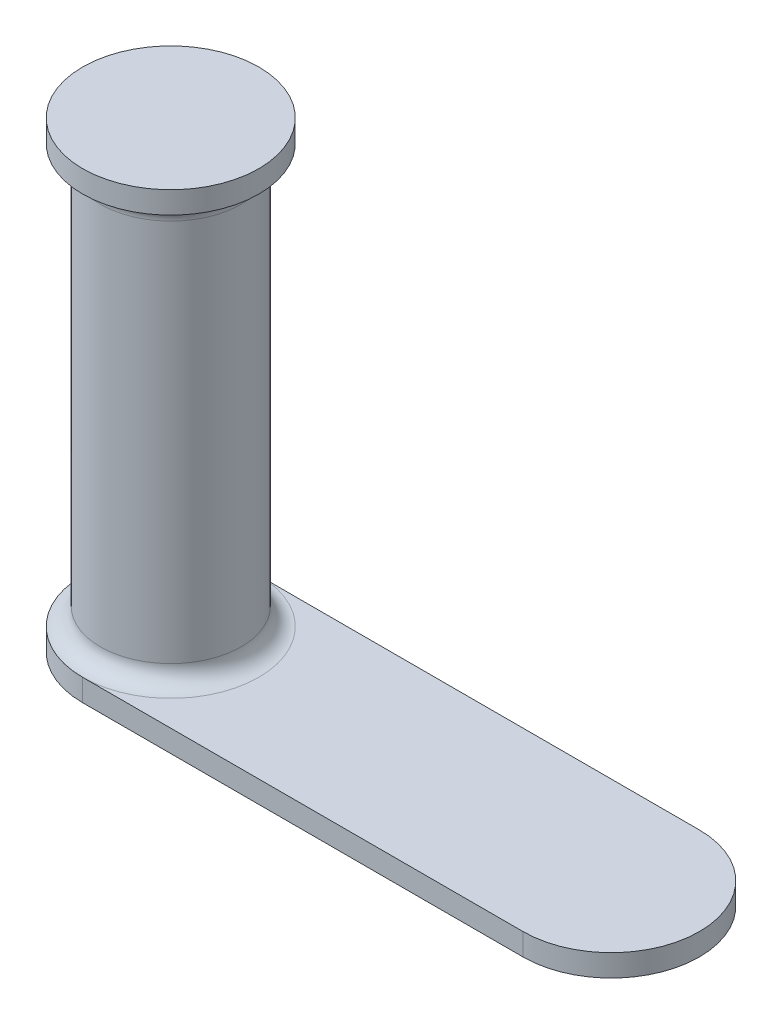
SolidWorks part; units mm, degrees
ref_plane "前视基准面" through (0, 0, 0) normal (0, 0, 1) x (1, 0, 0)
ref_plane "上视基准面" through (0, 0, 0) normal (0, 1, 0) x (1, 0, 0)
ref_plane "右视基准面" through (0, 0, 0) normal (1, 0, 0) x (0, 0, -1)
sketch "草图1" plane through (0, 0, 0) normal (0, 0, 1) x (1, 0, 0)
  line L0 (0, 60.1847) -> (0, -39.8153)
  line L1 (0, -39.8153) -> (20, -39.8153)
  line L2 (0, 60.1847) -> (20, 60.1847)
  line L3 (20, 60.1847) -> (20, 55.1847)
  line L5 (16, 51.1847) -> (16, -35.8153)
  arc A0 (20, 55.1847) -> (16, 51.1847) centre (20, 51.1847) ccw
  arc A1 (16, -35.8153) -> (20, -39.8153) centre (20, -35.8153) ccw
  dimension "D1" = 100
  dimension "D2" = 20
  dimension "D3" = 16
  dimension "D4" = 5
revolve "旋转1" add sketch "草图1" angle 360 about L0
sketch "草图2" plane through (0, -39.8153, 0) normal (0, -1, 0) x (1, 0, 0)
  line L0 (0, -20) -> (100, -20)
  line L2 (100, 20) -> (0, 20)
  arc A0 (0, 20) -> (0, -20) centre (0, 0) ccw
  arc A1 (100, -20) -> (100, 20) centre (100, 0) ccw
  dimension "D1" = 100
extrude "凸台-拉伸1" add sketch "草图2" along normal blind 5
